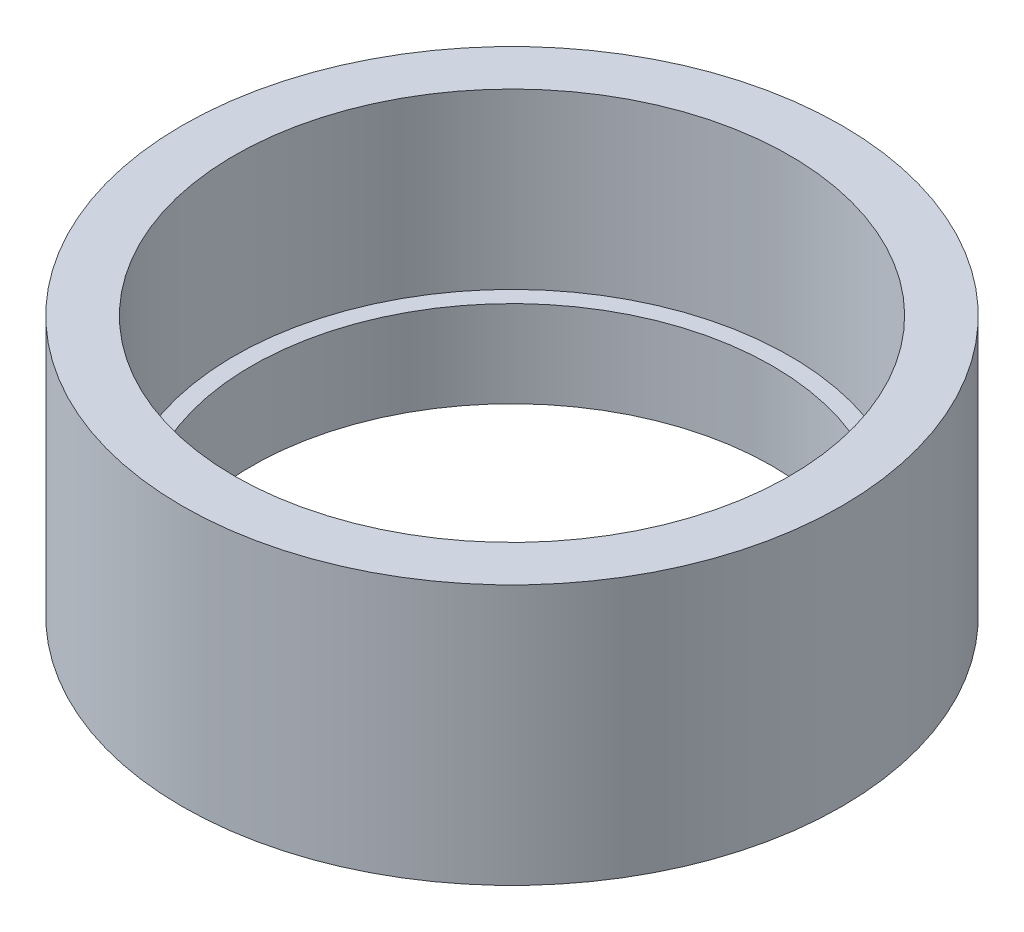
SolidWorks part; units mm, degrees
ref_plane "Front Plane" through (0, 0, 0) normal (0, 0, 1) x (1, 0, 0)
ref_plane "Top Plane" through (0, 0, 0) normal (0, 1, 0) x (1, 0, 0)
ref_plane "Right Plane" through (0, 0, 0) normal (1, 0, 0) x (0, 0, -1)
sketch "Sketch1" plane through (0, 0, 0) normal (0, 1, 0) x (1, 0, 0)
  circle A0 centre (0, 0) radius 3
  circle A1 centre (0, 0) radius 3.8
  dimension "D1" = 6
  dimension "D2" = 0.8
extrude "Boss-Extrude1" add sketch "Sketch1" along normal blind 1
sketch "Sketch2" plane through (0, 1, 0) normal (0, 1, 0) x (1, 0, 0)
  circle A0 centre (0, 0) radius 3.2
  circle A1 centre (0, 0) radius 3.8
  dimension "D1" = 6.4
extrude "Boss-Extrude2" add sketch "Sketch2" along normal blind 2
